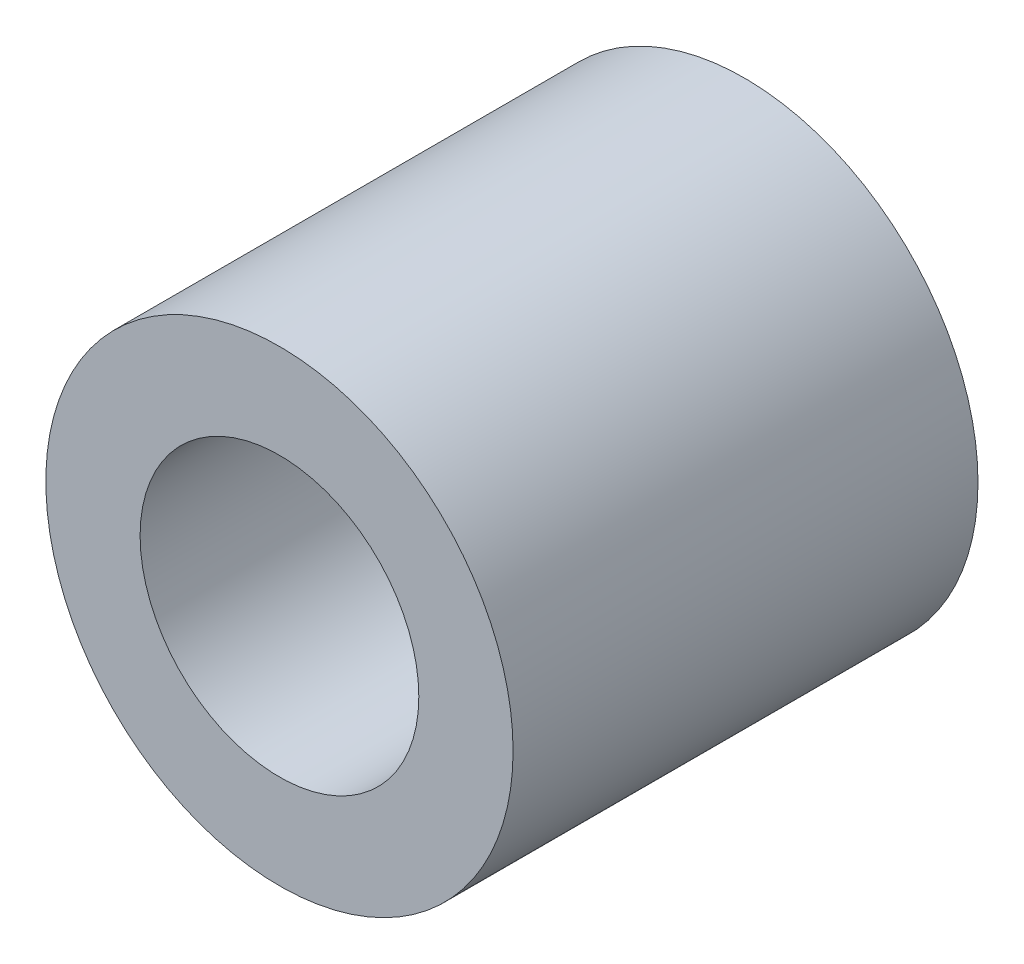
SolidWorks part; units mm, degrees
ref_plane "Front Plane" through (0, 0, 0) normal (0, 0, 1) x (1, 0, 0)
ref_plane "Top Plane" through (0, 0, 0) normal (0, 1, 0) x (1, 0, 0)
ref_plane "Right Plane" through (0, 0, 0) normal (1, 0, 0) x (0, 0, -1)
sketch "Sketch1" plane through (0, 0, 0) normal (0, 0, 1) x (1, 0, 0)
  circle A0 centre (0, 0) radius 5.995
  circle A1 centre (0, 0) radius 10.05
  dimension "D1" = 20.1
  dimension "D2" = 11.99
extrude "Boss-Extrude1" add sketch "Sketch1" along normal blind 20
